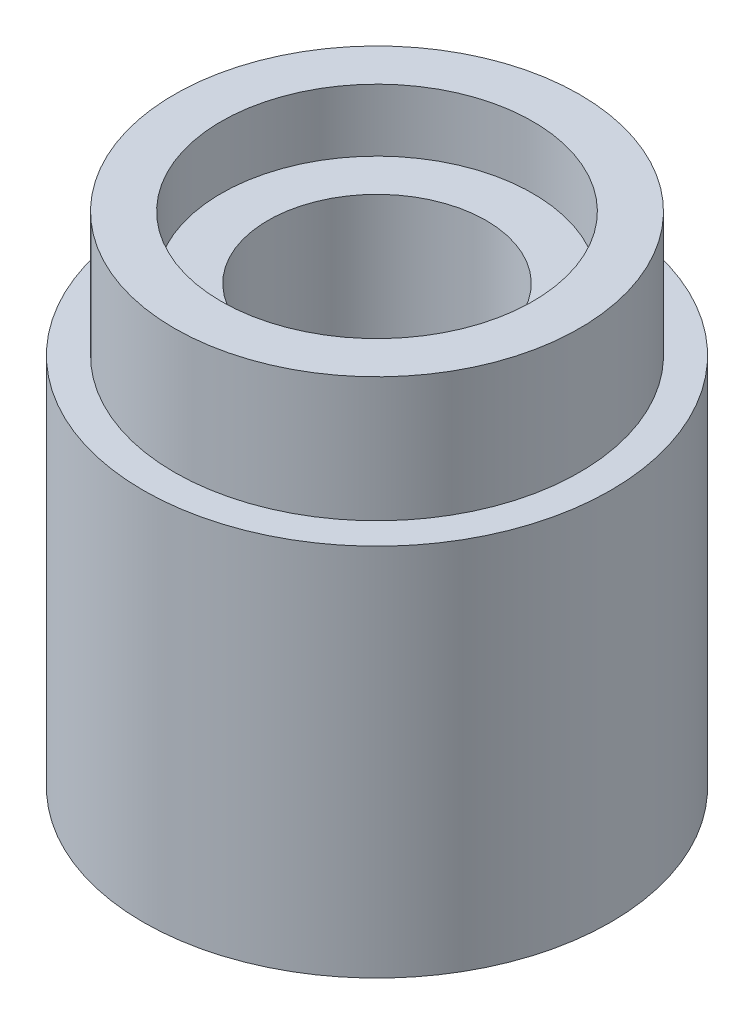
SolidWorks part; units mm, degrees
ref_plane "Front Plane" through (0, 0, 0) normal (0, 0, 1) x (1, 0, 0)
ref_plane "Top Plane" through (0, 0, 0) normal (0, 1, 0) x (1, 0, 0)
ref_plane "Right Plane" through (0, 0, 0) normal (1, 0, 0) x (0, 0, -1)
sketch "Sketch1" plane through (0, 0, 0) normal (0, 1, 0) x (1, 0, 0)
  circle A0 centre (0, 0) radius 3.75
extrude "Boss-Extrude1" add sketch "Sketch1" along normal blind 8
sketch "Sketch2" plane through (0, 8, 0) normal (0, 1, 0) x (1, 0, 0)
  circle A0 centre (0, 0) radius 2.5
  circle A1 centre (0, 0) radius 3.75
sketch "Sketch3" plane through (0, 8, 0) normal (0, 1, 0) x (1, 0, 0)
  circle A0 centre (0, 0) radius 3.25
  circle A1 centre (0, 0) radius 3.75
extrude "Cut-Extrude1" cut sketch "Sketch3" against normal blind 2
sketch "Sketch4" plane through (0, 8, 0) normal (0, 1, 0) x (1, 0, 0)
  circle A0 centre (0, 0) radius 1.75
extrude "Cut-Extrude2" cut sketch "Sketch4" against normal blind 7.5
sketch "Sketch5" plane through (0, 8, 0) normal (0, 1, 0) x (1, 0, 0)
  circle A0 centre (0, 0) radius 2.5
extrude "Cut-Extrude3" cut sketch "Sketch5" against normal blind 1
